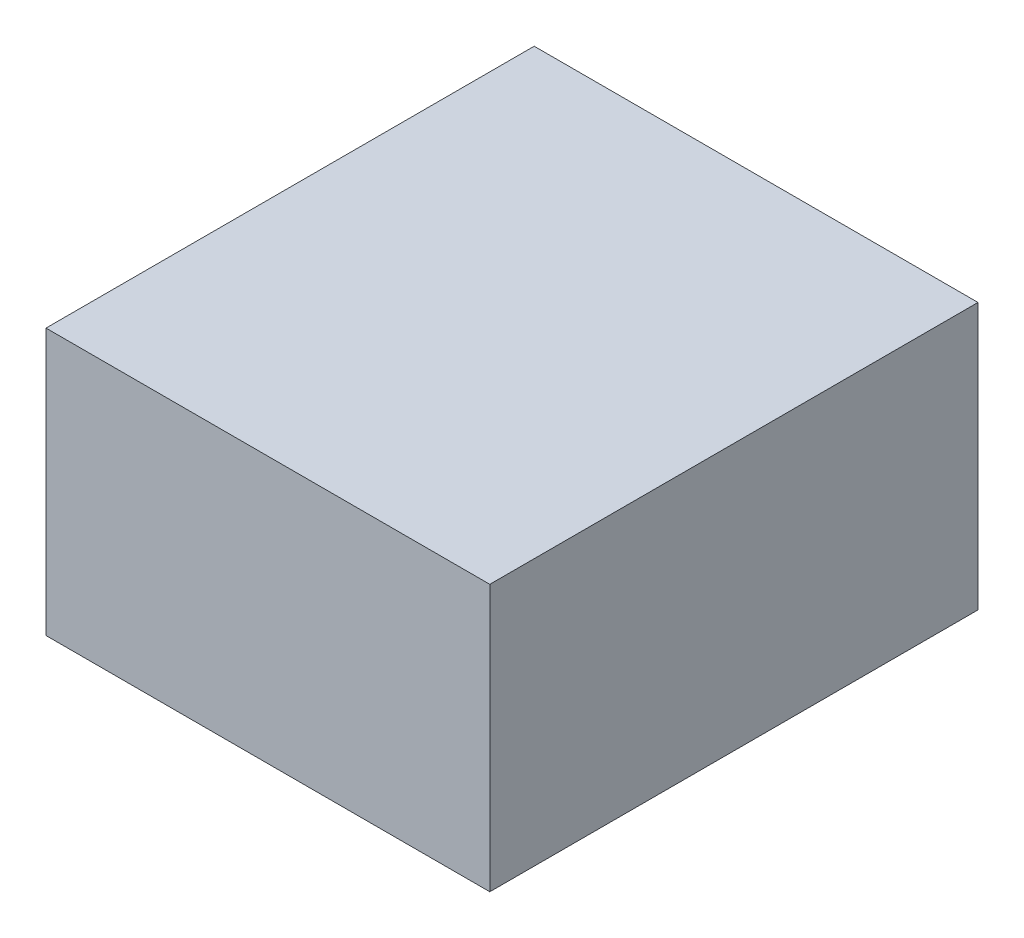
SolidWorks part; units mm, degrees
ref_plane "Piano frontale" through (0, 0, 0) normal (0, 0, 1) x (1, 0, 0)
ref_plane "Piano superiore" through (0, 0, 0) normal (0, 1, 0) x (1, 0, 0)
ref_plane "Piano destro" through (0, 0, 0) normal (1, 0, 0) x (0, 0, -1)
sketch "Schizzo1" plane through (0, 0, 0) normal (0, 0, 1) x (1, 0, 0)
  line L1 (-50, 30) -> (50, 30)
  line L2 (-50, 30) -> (-50, -30)
  line L3 (-50, -30) -> (50, -30)
  line L4 (50, 30) -> (50, -30)
  line L5 (-50, 30) -> (50, -30) construction
  line L6 (-50, -30) -> (50, 30) construction
  point P0 (0, 0)
  dimension "D1" = 100
  dimension "D2" = 60
extrude "Estrusione-Estrusione1" add sketch "Schizzo1" along normal blind 110
